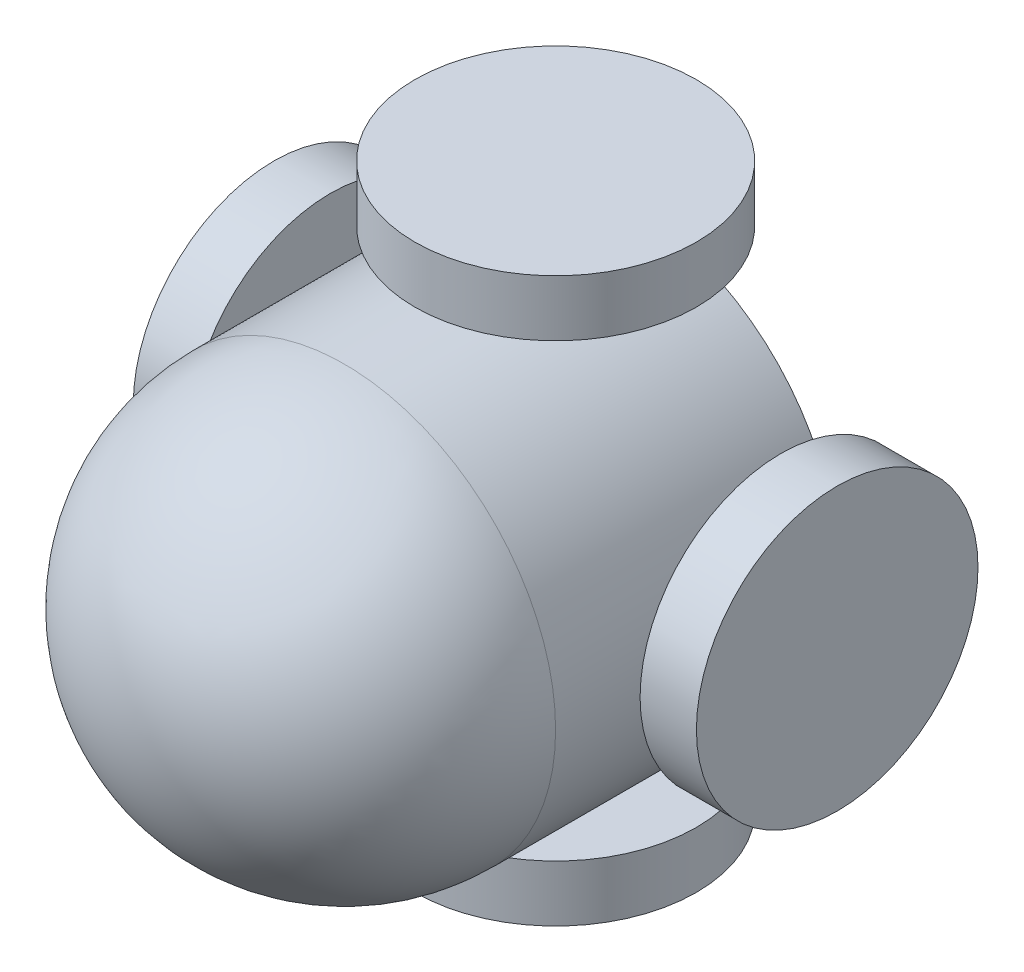
SolidWorks part; units mm, degrees
ref_plane "Front Plane" through (0, 0, 0) normal (0, 0, 1) x (1, 0, 0)
ref_plane "Top Plane" through (0, 0, 0) normal (0, 1, 0) x (1, 0, 0)
ref_plane "Right Plane" through (0, 0, 0) normal (1, 0, 0) x (0, 0, -1)
sketch "Sketch1" plane through (0, 0, 0) normal (0, 0, 1) x (1, 0, 0)
  circle A0 centre (0, 0) radius 1.5
  dimension "D1" = 3
extrude "Boss-Extrude1" add sketch "Sketch1" along normal blind 2 from offset 0.5
sketch "Sketch2" plane through (0, 0, 2.5) normal (0, 0, 1) x (1, 0, 0)
  line L0 (1.5, 0) -> (-1.5, 0)
  circle A0 centre (0, 0) radius 1.5 construction
  arc A1 (1.5, 0) -> (-1.5, 0) centre (0, 0) ccw
  point P6 (0, 0)
revolve "Revolve1" add sketch "Sketch2" angle 180 about L0
sketch "Sketch3" plane through (0, 0, 0) normal (1, 0, 0) x (0, 0, -1)
  line L0 (0, 0) -> (-1, 0) construction
  circle A1 centre (-1, 0) radius 0.25
  dimension "D1" = 0.5
  dimension "D2" = 1
extrude "Boss-Extrude2" add sketch "Sketch3" along normal blind 2
sketch "Sketch4" plane through (2, 0, 0) normal (1, 0, 0) x (0, 0, -1)
  circle A0 centre (-1, 0) radius 1
  dimension "D1" = 2
extrude "Boss-Extrude3" add sketch "Sketch4" against normal blind 0.4
pattern_circular "CirPattern2" count 4 every 90 about axis through (0, 0, 0) along (0, 0, 1) of "Boss-Extrude2", "Boss-Extrude3"
